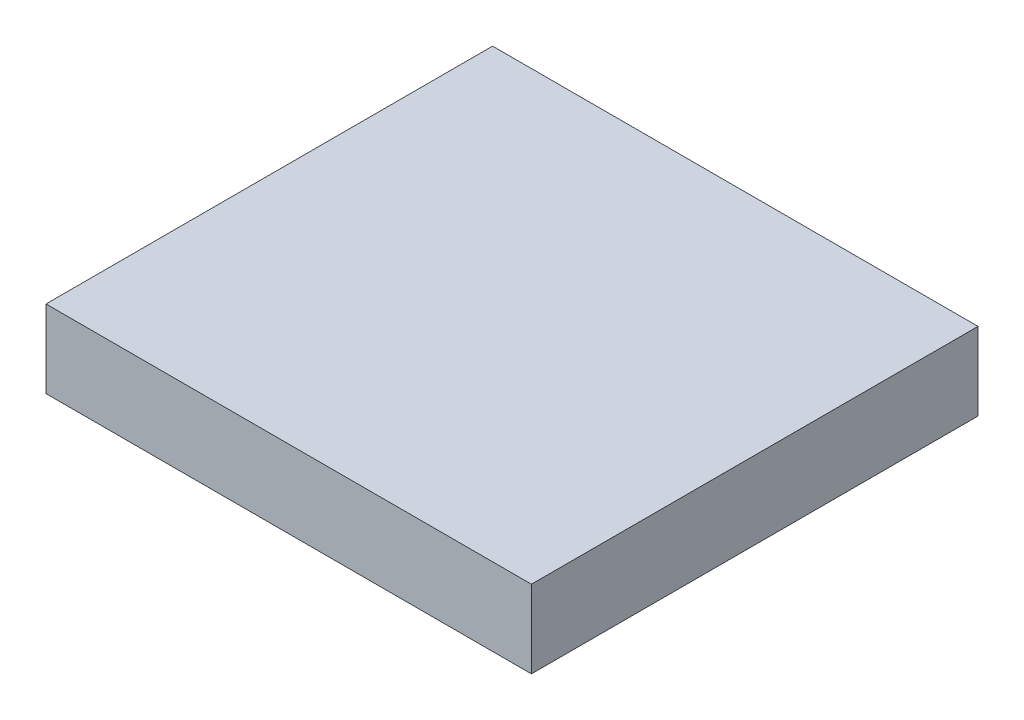
SolidWorks part; units mm, degrees
ref_plane "Front Plane" through (0, 0, 0) normal (0, 0, 1) x (1, 0, 0)
ref_plane "Top Plane" through (0, 0, 0) normal (0, 1, 0) x (1, 0, 0)
ref_plane "Right Plane" through (0, 0, 0) normal (1, 0, 0) x (0, 0, -1)
sketch "Sketch1" plane through (0, 0, 0) normal (0, 1, 0) x (1, 0, 0)
  line L1 (-250, 230) -> (250, 230)
  line L2 (-250, 230) -> (-250, -230)
  line L3 (-250, -230) -> (250, -230)
  line L4 (250, 230) -> (250, -230)
  line L5 (-250, 230) -> (250, -230) construction
  line L6 (-250, -230) -> (250, 230) construction
  point P0 (0, 0)
  dimension "D1" = 500
  dimension "D2" = 460
extrude "Boss-Extrude1" add sketch "Sketch1" along normal blind 80
